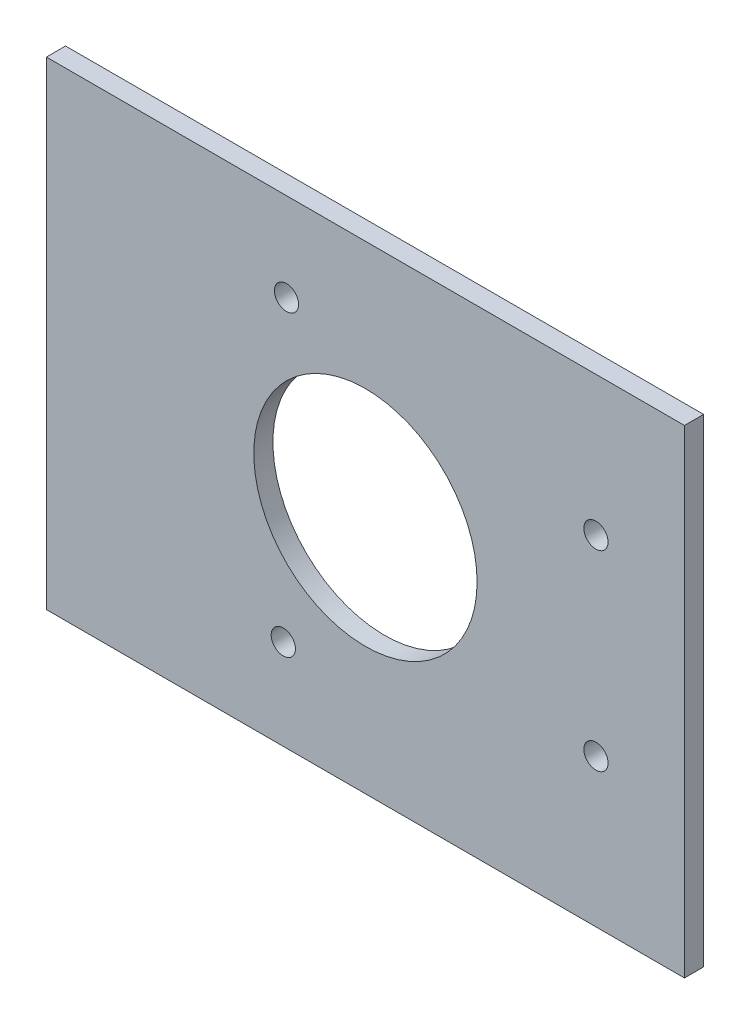
SolidWorks part; units mm, degrees
ref_plane "Front Plane" through (0, 0, 0) normal (0, 0, 1) x (1, 0, 0)
ref_plane "Top Plane" through (0, 0, 0) normal (0, 1, 0) x (1, 0, 0)
ref_plane "Right Plane" through (0, 0, 0) normal (1, 0, 0) x (0, 0, -1)
sketch "Croquis1" plane through (0, 0, 0) normal (0, 0, 1) x (1, 0, 0)
  line L1 (-50, 37.5) -> (50, 37.5)
  line L2 (-50, 37.5) -> (-50, -37.5)
  line L3 (-50, -37.5) -> (50, -37.5)
  line L4 (50, 37.5) -> (50, -37.5)
  circle A0 centre (0, 0) radius 17.5
  circle A3 centre (-12.8713, -23.3262) radius 1.9
  circle A4 centre (36.1287, -14.3262) radius 1.9
  circle A5 centre (36.1287, 15.6738) radius 1.9
  circle A6 centre (-12.3713, 23.6738) radius 1.9
  point P0 (0, 0)
  dimension "D5" = 35
  dimension "D1" = 100
  dimension "D2" = 75
  dimension "D3" = 37.5
  dimension "D4" = 50
extrude "Saliente-Extruir1" add sketch "Croquis1" along normal blind 3
